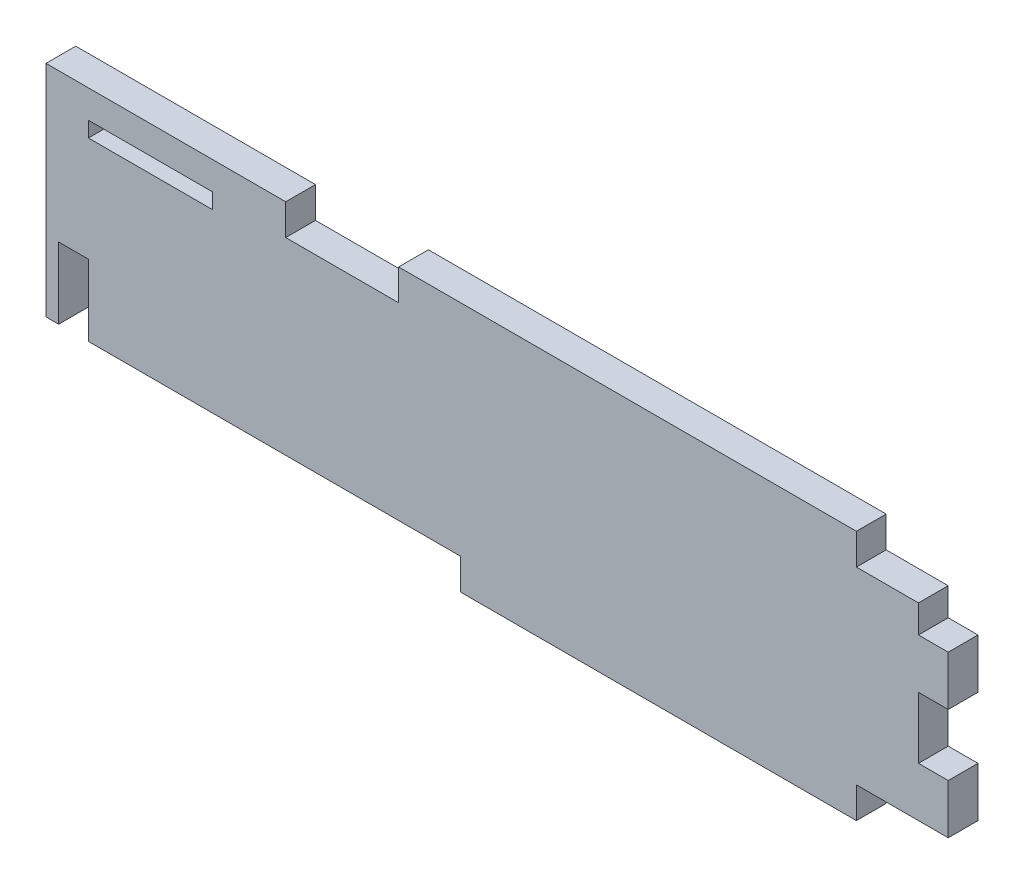
SolidWorks part; units mm, degrees
ref_plane "Front Plane" through (0, 0, 0) normal (0, 0, 1) x (1, 0, 0)
ref_plane "Top Plane" through (0, 0, 0) normal (0, 1, 0) x (1, 0, 0)
ref_plane "Right Plane" through (0, 0, 0) normal (1, 0, 0) x (0, 0, -1)
sketch "Sketch1" plane through (0, 0, 0) normal (0, 0, 1) x (1, 0, 0)
  line L0 (-6.35, 4.7244) -> (3.048, 4.7244) construction
  line L1 (-6.35, 4.7244) -> (-6.35, 1.5494) construction
  line L2 (-6.35, 1.5494) -> (-46.863, 1.5494) construction
  line L3 (-46.863, 1.5494) -> (-46.863, 4.7244) construction
  line L4 (-84.963, 24.3332) -> (-84.963, 22.7584) construction
  line L5 (-84.963, 22.7584) -> (-72.263, 22.7584) construction
  line L6 (-72.263, 22.7584) -> (-72.263, 24.3332) construction
  line L10 (-84.963, 24.3332) -> (-84.963, 22.7584)
  line L12 (-84.963, 22.7584) -> (-72.263, 22.7584)
  line L13 (-72.263, 22.7584) -> (-72.263, 24.3332)
  line L14 (-6.35, 27.2034) -> (-53.213, 27.2034) construction
  line L15 (-6.35, 24.0284) -> (-6.35, 27.2034) construction
  line L16 (0, 24.0284) -> (-6.35, 24.0284) construction
  line L17 (0, 24.0284) -> (0, 21.1836) construction
  line L18 (3.048, 21.1836) -> (0, 21.1836) construction
  line L19 (3.048, 21.1836) -> (3.048, 16.1036) construction
  line L20 (3.048, 16.1036) -> (0, 16.1036) construction
  line L21 (0, 16.1036) -> (0, 9.8044) construction
  line L22 (3.048, 9.8044) -> (0, 9.8044) construction
  line L23 (3.048, 9.8044) -> (3.048, 4.7244) construction
  line L24 (-6.35, 4.7244) -> (3.048, 4.7244)
  line L25 (-6.35, 4.7244) -> (-6.35, 1.5494)
  line L26 (-6.35, 1.5494) -> (-46.863, 1.5494)
  line L27 (-46.863, 1.5494) -> (-46.863, 4.7244)
  line L28 (-84.963, 4.7244) -> (-46.863, 4.7244)
  line L29 (-89.3064, 15.9639) -> (-89.3064, 4.7244)
  line L30 (-89.3064, 4.7244) -> (-86.7664, 4.7244)
  line L32 (-86.7664, 4.7244) -> (-86.7664, 12.0142)
  line L33 (-64.77, 24.0284) -> (-53.213, 24.0284)
  line L34 (-86.7664, 12.0142) -> (-84.963, 12.0142)
  line L35 (-84.963, 12.0142) -> (-84.963, 4.7244)
  line L36 (-72.263, 24.3332) -> (-84.963, 24.3332)
  line L37 (-53.213, 27.2034) -> (-53.213, 24.0284)
  line L38 (-6.35, 27.2034) -> (-53.213, 27.2034)
  line L39 (-6.35, 24.0284) -> (-6.35, 27.2034)
  line L40 (0, 24.0284) -> (-6.35, 24.0284)
  line L41 (0, 24.0284) -> (0, 21.1836)
  line L42 (3.048, 21.1836) -> (0, 21.1836)
  line L43 (3.048, 21.1836) -> (3.048, 16.1036)
  line L44 (3.048, 16.1036) -> (0, 16.1036)
  line L45 (0, 16.1036) -> (0, 9.8044)
  line L46 (3.048, 9.8044) -> (0, 9.8044)
  line L47 (3.048, 9.8044) -> (3.048, 4.7244)
  line L48 (-89.3064, 4.7244) -> (-89.3064, 27.2034) construction
  line L49 (-89.3064, 27.2034) -> (-64.77, 27.2034) construction
  line L50 (-64.77, 27.2034) -> (-64.77, 24.0284) construction
  line L51 (-89.3064, 4.7244) -> (-89.3064, 27.2034)
  line L52 (-89.3064, 27.2034) -> (-64.77, 27.2034)
  line L53 (-64.77, 27.2034) -> (-64.77, 24.0284)
extrude "Boss-Extrude1" add sketch "Sketch1" along normal blind 3.048
sketch "Sketch2" plane through (0, 0, 3.048) normal (0, 0, 1) x (1, 0, 0)
  line L1 (-72.263, 24.3332) -> (-84.963, 24.3332) construction
  line L2 (-84.963, 24.3332) -> (-72.263, 24.3332)
  line L3 (-84.963, 24.3332) -> (-84.963, 24.4348)
  line L4 (-84.963, 24.4348) -> (-72.263, 24.4348)
  line L6 (-72.263, 24.3332) -> (-72.263, 24.4348)
  line L7 (-84.963, 22.7584) -> (-72.263, 22.7584) construction
  dimension "D1" = 1.6764
extrude "Boss-Extrude2" add sketch "Sketch2" against normal up to vertex (3.048 mm away) up to point (-64.77, 27.2034, 0)
sketch "Sketch3" plane through (0, 0, 3.048) normal (0, 0, 1) x (1, 0, 0)
  line L1 (-88.011, 12.0142) -> (-84.963, 12.0142)
  line L2 (-88.011, 12.0142) -> (-88.011, 4.7244)
  line L3 (-88.011, 4.7244) -> (-84.963, 4.7244)
  line L4 (-84.963, 12.0142) -> (-84.963, 4.7244)
extrude "Cut-Extrude1" cut sketch "Sketch3" against normal through all
